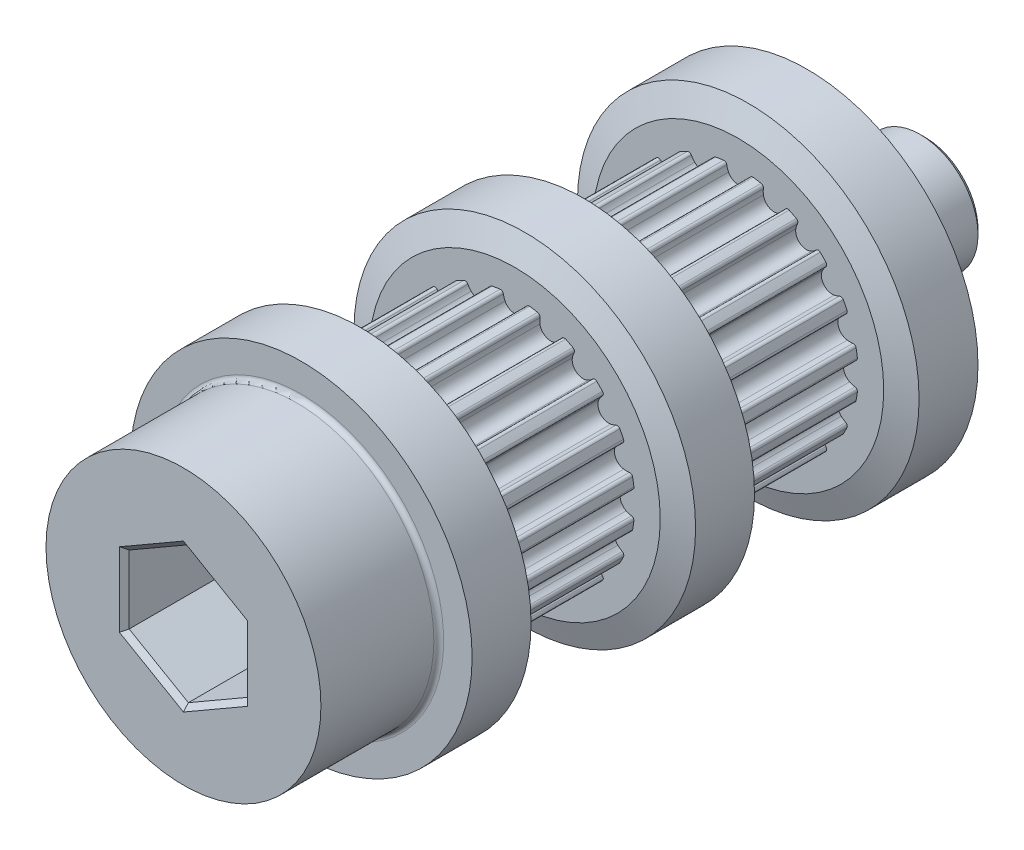
SolidWorks part; units mm, degrees
ref_plane "Front Plane" through (0, 0, 0) normal (0, 0, 1) x (1, 0, 0)
ref_plane "Top Plane" through (0, 0, 0) normal (0, 1, 0) x (1, 0, 0)
ref_plane "Right Plane" through (0, 0, 0) normal (1, 0, 0) x (0, 0, -1)
sketch "Sketch1" plane through (0, 0, 0) normal (0, 0, 1) x (1, 0, 0)
  line B0 (-1.7499, 5.3585) -> (1.7499, 5.3585) construction
  line B1 (0, 0) -> (0, 5.3585) construction
  line B2 (0, 5.3585) -> (0, 11.2111) construction
  line B3 (0, 6.3625) -> (1.9751, 6.0482) construction
  line B4 (1.9751, 6.0482) -> (2.6648, 5.8229) construction
  line B5 (1.9751, 6.0482) -> (1.7499, 5.3585) construction
  line B6 (-1.9751, 6.0482) -> (-1.7499, 5.3585) construction
  line B7 (-1.8963, 5.8067) -> (-2.841, 8.6995)
  line B8 (-2.841, 8.6995) -> (2.841, 8.6995)
  line B9 (2.841, 8.6995) -> (1.8963, 5.8067)
  circle B10 centre (0, 0) radius 6.3625 construction
  circle B11 centre (0, 0) radius 8.6995 construction
  circle B12 centre (0, 0) radius 6.1085 construction
  arc B13 (-0.4989, 5.6703) -> (0.4989, 5.6703) centre (0, 5.9135) ccw
  arc B14 (-0.4989, 5.6703) -> (-0.5855, 5.9387) centre (0.4, 6.1085) cw
  arc B15 (-1.8963, 5.8067) -> (-0.7518, 6.0621) centre (0, 0) cw
  arc B16 (-0.5855, 5.9387) -> (-0.7518, 6.0621) centre (-0.7333, 5.9132) ccw
  arc B17 (1.8963, 5.8067) -> (0.7518, 6.0621) centre (0, 0) ccw
  arc B18 (0.5855, 5.9387) -> (0.7518, 6.0621) centre (0.7333, 5.9132) cw
  arc B19 (0.4989, 5.6703) -> (0.5855, 5.9387) centre (-0.4, 6.1085) ccw
sketch_block_instance "Block-Gt Timing Belt Pulley Groove-1"
sketch_block "Block-Gt Timing Belt Pulley Groove" parameters "D1"=12.725, "D2"=17.399, "D6"=0.555, "D7"=1, "D9"=0.15, "D3"=9.6972, "D4"=4.8486, "D5"=2, "D8"=0.254, "D10"=0.4, "D11"=0.75
sketch "Sketch9" plane through (0, 0, 0) normal (0, 0, 1) x (1, 0, 0)
  line L1 (0, 3.1927) -> (-2.765, 1.5964) construction
  line L2 (-2.765, 1.5964) -> (-2.765, -1.5964) construction
  line L3 (-2.765, -1.5964) -> (0, -3.1927) construction
  line L4 (0, -3.1927) -> (2.765, -1.5964) construction
  line L5 (2.765, -1.5964) -> (2.765, 1.5964) construction
  line L6 (2.765, 1.5964) -> (0, 3.1927) construction
  circle A0 centre (0, 0) radius 2.765 construction
  dimension "D1" = 5.53
sketch "Sketch2" plane through (0, 0, 0) normal (1, 0, 0) x (0, 0, -1)
  line L0 (-3.685, 6.1085) -> (3.685, 6.1085)
  line L1 (-18.57, 0) -> (7.19, 0) construction
  line L2 (-3.685, 6.1085) -> (-3.685, 7.404)
  line L3 (-3.685, 7.404) -> (-4.19, 8.6995)
  line L4 (-4.19, 8.6995) -> (-7.19, 8.6995)
  line L5 (-7.19, 8.6995) -> (-7.695, 7.404)
  line L6 (3.685, 6.1085) -> (3.685, 7.404)
  line L7 (3.685, 7.404) -> (4.19, 8.6995)
  line L8 (4.19, 8.6995) -> (7.19, 8.6995)
  line L9 (7.19, 8.6995) -> (7.19, 0)
  line L10 (0, 6.1085) -> (0, 0) construction
  line L11 (-18.57, 0) -> (7.19, 0)
  line L12 (-7.695, 7.404) -> (-7.695, 6.1085)
  line L13 (-7.695, 6.1085) -> (-15.065, 6.1085)
  line L14 (-15.065, 6.1085) -> (-15.065, 7.404)
  line L15 (-15.065, 7.404) -> (-15.57, 8.6995)
  line L16 (-15.57, 8.6995) -> (-18.57, 8.6995)
  line L17 (-18.57, 8.6995) -> (-18.57, 0)
  dimension "D1" = 12.217
  dimension "D2" = 7.37
  dimension "D3" = 8.38
  dimension "D4" = 17.399
  dimension "D5" = 14.808
  dimension "D6" = 3
revolve "Revolve1" add sketch "Sketch2" angle 360 about L11
sketch "Sketch10" plane through (0, 0, 18.57) normal (0, 0, 1) x (1, 0, 0)
  circle A0 centre (0, 0) radius 7
  dimension "D1" = 14
extrude "Boss-Extrude1" add sketch "Sketch10" along normal blind 6
sketch "Sketch13" plane through (0, 0, -7.19) normal (0, 0, -1) x (-1, 0, 0)
  circle A0 centre (0, 0) radius 2.95
  dimension "D1" = 5.9
extrude "Boss-Extrude2" add sketch "Sketch13" along normal blind 6
sketch "Sketch5" plane through (0, 0, 0) normal (0, 0, 1) x (1, 0, 0)
  line L0 (2.841, 8.6995) -> (1.8963, 5.8067) construction
  line L1 (-1.8963, 5.8067) -> (-2.841, 8.6995) construction
  line L2 (-2.841, 8.6995) -> (2.841, 8.6995) construction
  line L3 (2.841, 8.6995) -> (1.8963, 5.8067)
  line L4 (-1.8963, 5.8067) -> (-2.841, 8.6995)
  line L5 (-2.841, 8.6995) -> (2.841, 8.6995)
  arc A0 (1.8963, 5.8067) -> (0.7518, 6.0621) centre (0, 0) ccw construction
  arc A1 (0.7518, 6.0621) -> (0.5855, 5.9387) centre (0.7333, 5.9132) ccw construction
  arc A2 (0.4989, 5.6703) -> (0.5855, 5.9387) centre (-0.4, 6.1085) ccw construction
  arc A3 (-0.4989, 5.6703) -> (0.4989, 5.6703) centre (0, 5.9135) ccw construction
  arc A4 (-0.5855, 5.9387) -> (-0.4989, 5.6703) centre (0.4, 6.1085) ccw construction
  arc A5 (-0.5855, 5.9387) -> (-0.7518, 6.0621) centre (-0.7333, 5.9132) ccw construction
  arc A6 (-0.7518, 6.0621) -> (-1.8963, 5.8067) centre (0, 0) ccw construction
  arc A7 (1.8963, 5.8067) -> (0.7518, 6.0621) centre (0, 0) ccw
  arc A8 (0.7518, 6.0621) -> (0.5855, 5.9387) centre (0.7333, 5.9132) ccw
  arc A9 (0.4989, 5.6703) -> (0.5855, 5.9387) centre (-0.4, 6.1085) ccw
  arc A10 (-0.4989, 5.6703) -> (0.4989, 5.6703) centre (0, 5.9135) ccw
  arc A11 (-0.5855, 5.9387) -> (-0.4989, 5.6703) centre (0.4, 6.1085) ccw
  arc A12 (-0.5855, 5.9387) -> (-0.7518, 6.0621) centre (-0.7333, 5.9132) ccw
  arc A13 (-0.7518, 6.0621) -> (-1.8963, 5.8067) centre (0, 0) ccw
extrude "Cut-Extrude1" cut sketch "Sketch5" against normal up to surface (3.685 mm away) and the other way up to surface (3.685 mm away) up to face at (6.1085, 0, -3.685) other way up to face at (7.404, 0, 3.685)
sketch "Sketch7" plane through (0, 0, 7.695) normal (0, 0, 1) x (1, 0, 0)
  line L3 (1.8963, 5.8067) -> (2.841, 8.6995)
  line L4 (2.841, 8.6995) -> (-2.841, 8.6995)
  line L5 (-2.841, 8.6995) -> (-1.8963, 5.8067)
  line L6 (1.8963, 5.8067) -> (2.841, 8.6995)
  line L7 (2.841, 8.6995) -> (-2.841, 8.6995)
  line L8 (-2.841, 8.6995) -> (-1.8963, 5.8067)
  arc A7 (-0.7518, 6.0621) -> (-1.8963, 5.8067) centre (0, 0) ccw
  arc A8 (-0.5855, 5.9387) -> (-0.7518, 6.0621) centre (-0.7333, 5.9132) ccw
  arc A9 (-0.5855, 5.9387) -> (-0.4989, 5.6703) centre (0.4, 6.1085) ccw
  arc A10 (-0.4989, 5.6703) -> (0.4989, 5.6703) centre (0, 5.9135) ccw
  arc A11 (0.4989, 5.6703) -> (0.5855, 5.9387) centre (-0.4, 6.1085) ccw
  arc A12 (0.7518, 6.0621) -> (0.5855, 5.9387) centre (0.7333, 5.9132) ccw
  arc A13 (1.8963, 5.8067) -> (0.7518, 6.0621) centre (0, 0) ccw
  arc A14 (-0.7518, 6.0621) -> (-1.8963, 5.8067) centre (0, 0) ccw
  arc A15 (-0.5855, 5.9387) -> (-0.7518, 6.0621) centre (-0.7333, 5.9132) ccw
  arc A16 (-0.5855, 5.9387) -> (-0.4989, 5.6703) centre (0.4, 6.1085) ccw
  arc A17 (-0.4989, 5.6703) -> (0.4989, 5.6703) centre (0, 5.9135) ccw
  arc A18 (0.4989, 5.6703) -> (0.5855, 5.9387) centre (-0.4, 6.1085) ccw
  arc A19 (0.7518, 6.0621) -> (0.5855, 5.9387) centre (0.7333, 5.9132) ccw
  arc A20 (1.8963, 5.8067) -> (0.7518, 6.0621) centre (0, 0) ccw
  dimension "D1" = 0
extrude "Cut-Extrude3" cut sketch "Sketch7" along normal up to surface (7.37 mm away) up to face at (7.404, 0, 15.065)
pattern_circular "CirPattern1" count 20 over 360 about axis through (0, 0, 0) along (0, 0, 1) of "Cut-Extrude1", "Cut-Extrude3"
sketch "Sketch11" plane through (0, 0, 18.57) normal (0, 0, 1) x (1, 0, 0)
  line L24 (0, 3.4814) -> (-3.015, 1.7407)
  line L25 (-3.015, 1.7407) -> (-3.015, -1.7407)
  line L26 (-3.015, -1.7407) -> (0, -3.4814)
  line L27 (0, -3.4814) -> (3.015, -1.7407)
  line L28 (3.015, -1.7407) -> (3.015, 1.7407)
  line L29 (3.015, 1.7407) -> (0, 3.4814)
  line L30 (0, 3.4814) -> (-3.015, 1.7407)
  line L31 (-3.015, 1.7407) -> (-3.015, -1.7407)
  line L32 (-3.015, -1.7407) -> (0, -3.4814)
  line L33 (0, -3.4814) -> (3.015, -1.7407)
  line L34 (3.015, -1.7407) -> (3.015, 1.7407)
  line L35 (3.015, 1.7407) -> (0, 3.4814)
  dimension "D1" = 0.25
extrude "Cut-Extrude4" cut sketch "Sketch11" along normal through all
fillet "Fillet1" radius 0.25 2 edges at (7, 0, 18.57) (-2.95, 0, -7.19)
chamfer "Chamfer1" distance 0.25 angle 45 7 edges at (-2.95, 0, -13.19) (-3.015, 0, 24.57) (-1.5075, 2.6111, 24.57) (1.5075, 2.6111, 24.57) (3.015, 0, 24.57) (1.5075, -2.6111, 24.57) (-1.5075, -2.6111, 24.57)
ref_plane "Plane1" through (0, 0, 0) normal (0, 0, 1) x (1, 0, 0)
ref_plane "Plane2" through (0, 0, 11.38) normal (0, 0, 1) x (1, 0, 0)
